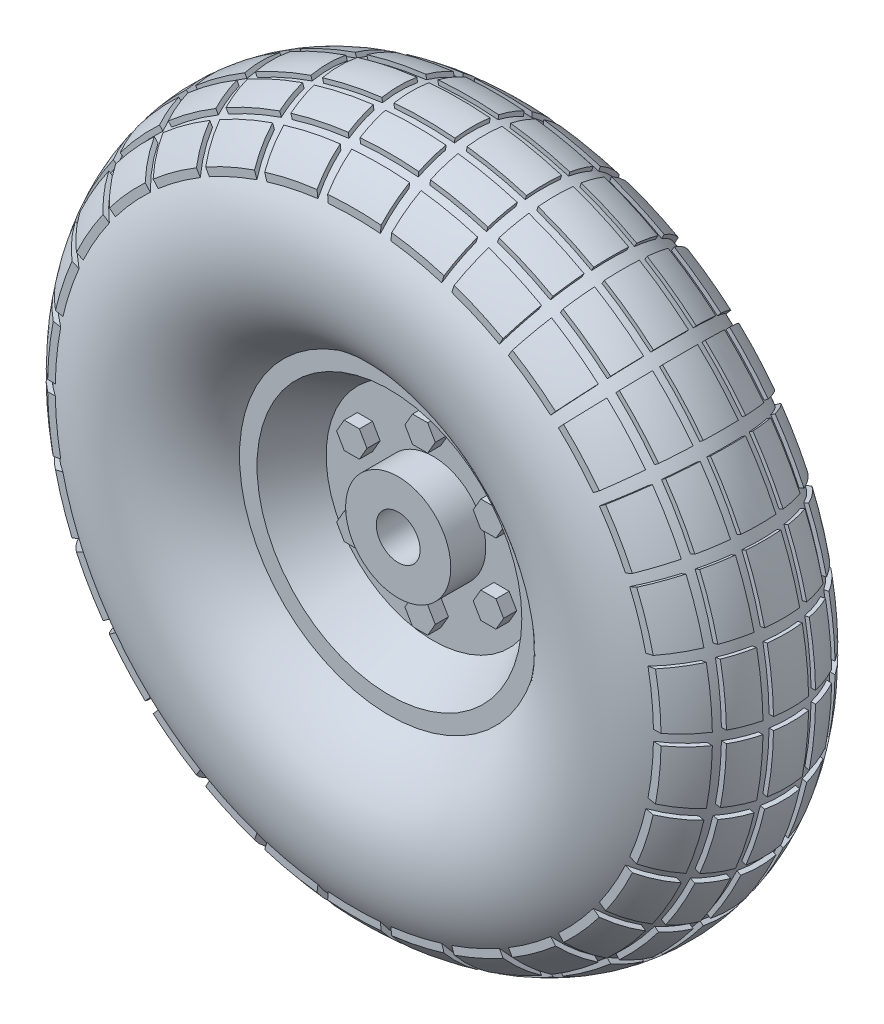
SolidWorks part; units mm, degrees
ref_plane "Front Plane" through (0, 0, 0) normal (0, 0, 1) x (1, 0, 0)
ref_plane "Top Plane" through (0, 0, 0) normal (0, 1, 0) x (1, 0, 0)
ref_plane "Right Plane" through (0, 0, 0) normal (1, 0, 0) x (0, 0, -1)
sketch "Sketch1" plane through (0, 0, 0) normal (1, 0, 0) x (0, 0, -1)
  line L0 (-19.05, 47.9669) -> (-19.05, 54.3169)
  line L1 (-19.05, 47.9669) -> (-3.175, 38.8015)
  line L2 (-3.175, 38.8015) -> (-3.175, 0)
  line L3 (-3.175, 0) -> (0, 0)
  line L4 (0, 0) -> (0, 52.3875)
  line L5 (0, 122.2375) -> (0, 125.4125)
  arc A0 (0, 125.4125) -> (-19.05, 54.3169) centre (0, 87.3125) ccw
  arc A1 (0, 122.2375) -> (0, 52.3875) centre (0, 87.3125) ccw
  dimension "D1" = 3.175
  dimension "D6" = 76.2
  dimension "D2" = 120
  dimension "D3" = 6.35
  dimension "D4" = 3.175
  dimension "D5" = 125.4125
  dimension "D7" = 19.05
revolve "Revolve1" add sketch "Sketch1" angle 360 about L3
sketch "Sketch3" plane through (0, 0, 0) normal (1, 0, 0) x (0, 0, -1)
  line L0 (0, 125.4125) -> (0, 127)
  line L1 (-9.525, 125.84) -> (-9.525, 124.2027)
  line L3 (-19.05, 122.1291) -> (-19.05, 120.3081)
  line L5 (-22.225, 120.1933) -> (-22.225, 118.2586)
  line L7 (-31.75, 111.125) -> (-31.75, 108.3731)
  line L8 (-6.35, 126.4887) -> (-6.35, 124.8796)
  arc A0 (-19.05, -49.5544) -> (0, -120.65) centre (0, -82.55) ccw
  arc A1 (0, 127) -> (-6.35, 126.4887) centre (0, 87.3125) ccw
  arc A2 (0, 125.4125) -> (-19.05, 54.3169) centre (0, 87.3125) ccw
  arc A3 (0, 125.4125) -> (-6.35, 124.8796) centre (0, 87.3125) ccw
  arc A4 (-22.225, 118.2586) -> (-31.75, 108.3731) centre (0, 87.3125) ccw
  arc A5 (-9.525, 124.2027) -> (-19.05, 120.3081) centre (0, 87.3125) ccw
  arc A6 (-9.525, 125.84) -> (-19.05, 122.1291) centre (0, 87.3125) ccw
  arc A7 (-22.225, 120.1933) -> (-31.75, 111.125) centre (0, 87.3125) ccw
  dimension "D1" = 6.35
  dimension "D2" = 3.175
  dimension "D3" = 3.175
  dimension "D4" = 9.525
  dimension "D5" = 9.525
  dimension "D6" = 127
revolve "Revolve2" add sketch "Sketch3" angle 10 mid plane about axis through (0, 0, 3.175) along (0, 0, -1)
pattern_circular "CirPattern1" count 30 over 360 about axis through (0, 0, 0) along (0, 0, 1) of "Revolve2"
sketch "Sketch4" plane through (0, 0, 3.175) normal (0, 0, 1) x (1, 0, 0)
  line L1 (5.4993, 28.575) -> (2.7496, 33.3375)
  line L2 (2.7496, 33.3375) -> (-2.7496, 33.3375)
  line L3 (-2.7496, 33.3375) -> (-5.4993, 28.575)
  line L4 (-5.4993, 28.575) -> (-2.7496, 23.8125)
  line L5 (-2.7496, 23.8125) -> (2.7496, 23.8125)
  line L6 (2.7496, 23.8125) -> (5.4993, 28.575)
  circle A0 centre (0, 28.575) radius 4.7625 construction
  dimension "D1" = 9.525
  dimension "D2" = 28.575
extrude "Extrude1" add sketch "Sketch4" along normal blind 4.7625
pattern_circular "CirPattern2" count 6 over 360 about axis through (0, 0, 0) along (0, 0, 1) of "Extrude1"
sketch "Sketch6" plane through (0, 0, 3.175) normal (0, 0, 1) x (1, 0, 0)
  circle A0 centre (0, 0) radius 19.05
  dimension "D1" = 38.1
extrude "Extrude3" add sketch "Sketch6" along normal blind 12.7
sketch "Sketch7" plane through (0, 0, 15.875) normal (0, 0, 1) x (1, 0, 0)
  circle A0 centre (0, 0) radius 7.9375
  dimension "D1" = 15.875
extrude "Cut-Extrude1" cut sketch "Sketch7" against normal through all
mirror "Mirror1" about plane through (0, 0, 0) normal (0, 0, 1) of "Cut-Extrude1", "Extrude3", "CirPattern2", "Extrude1", "CirPattern1", "Revolve2", "Revolve1"
sketch "Sketch5" plane through (0, 0, -7.9375) normal (0, 0, -1) x (-1, 0, 0)
  line L0 (2.7496, 33.3375) -> (-2.7496, 23.8125) construction
  circle A0 centre (0, 28.575) radius 2.54
  dimension "D1" = 5.08
extrude "Extrude2" add sketch "Sketch5" along normal blind 6.35
pattern_circular "CirPattern3" count 6 over 360 about axis through (0, 0, 0) along (0, 0, 1) of "Extrude2"
